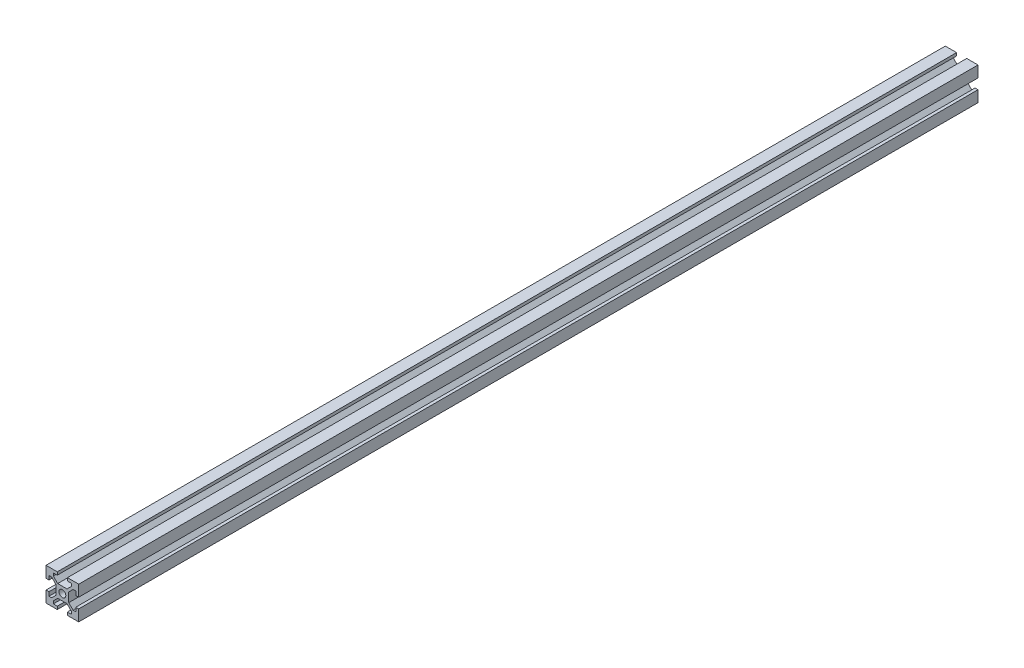
SolidWorks part; units mm, degrees
ref_plane "Front Plane" through (0, 0, 0) normal (0, 0, 1) x (1, 0, 0)
ref_plane "Top Plane" through (0, 0, 0) normal (0, 1, 0) x (1, 0, 0)
ref_plane "Right Plane" through (0, 0, 0) normal (1, 0, 0) x (0, 0, -1)
sketch "Sketch1" plane through (0, 0, 0) normal (0, 0, 1) x (1, 0, 0)
  line L0 (-3.1, 10) -> (-3.1, 8.2007)
  line L1 (-10, 10) -> (-3.1, 10)
  line L2 (-10, 10) -> (-10, 3.1)
  line L3 (-10, -10) -> (-3.1, -10)
  line L4 (10, 10) -> (10, 3.1)
  line L5 (-10, 10) -> (10, -10) construction
  line L6 (-10, -10) -> (10, 10) construction
  line L7 (-3.1, 8.2007) -> (-5.5, 8.2007)
  line L8 (-5.5, 8.2007) -> (-5.5, 6.5607)
  line L9 (-5.5, 6.5607) -> (-2.84, 3.9007)
  line L10 (-2.84, 3.9007) -> (2.84, 3.9007)
  line L11 (2.84, 3.9007) -> (5.5, 6.5607)
  line L12 (5.5, 6.5607) -> (5.5, 8.2007)
  line L13 (5.5, 8.2007) -> (3.1, 8.2007)
  line L14 (3.1, 8.2007) -> (3.1, 10)
  line L15 (-3.1, 8.2007) -> (3.1, 8.2007) construction
  line L16 (-5.5, 6.5607) -> (5.5, 6.5607) construction
  line L17 (3.1, 10) -> (10, 10)
  line L18 (8.2007, 3.1) -> (8.2007, 5.5)
  line L19 (8.2007, 5.5) -> (6.5607, 5.5)
  line L20 (6.5607, 5.5) -> (3.9007, 2.84)
  line L21 (3.9007, 2.84) -> (3.9007, -2.84)
  line L22 (3.9007, -2.84) -> (6.5607, -5.5)
  line L23 (6.5607, -5.5) -> (8.2007, -5.5)
  line L24 (8.2007, -5.5) -> (8.2007, -3.1)
  line L25 (8.2007, 3.1) -> (8.2007, -3.1) construction
  line L26 (6.5607, 5.5) -> (6.5607, -5.5) construction
  line L27 (10, 3.1) -> (8.2007, 3.1)
  line L28 (8.2007, -3.1) -> (10, -3.1)
  line L29 (3.1, -8.2007) -> (5.5, -8.2007)
  line L30 (5.5, -8.2007) -> (5.5, -6.5607)
  line L31 (5.5, -6.5607) -> (2.84, -3.9007)
  line L32 (2.84, -3.9007) -> (-2.84, -3.9007)
  line L33 (-2.84, -3.9007) -> (-5.5, -6.5607)
  line L34 (-5.5, -6.5607) -> (-5.5, -8.2007)
  line L35 (-5.5, -8.2007) -> (-3.1, -8.2007)
  line L36 (3.1, -8.2007) -> (-3.1, -8.2007) construction
  line L37 (5.5, -6.5607) -> (-5.5, -6.5607) construction
  line L38 (3.1, -10) -> (3.1, -8.2007)
  line L39 (-3.1, -8.2007) -> (-3.1, -10)
  line L40 (-8.2007, -3.1) -> (-8.2007, -5.5)
  line L41 (-8.2007, -5.5) -> (-6.5607, -5.5)
  line L42 (-6.5607, -5.5) -> (-3.9007, -2.84)
  line L43 (-3.9007, -2.84) -> (-3.9007, 2.84)
  line L44 (-3.9007, 2.84) -> (-6.5607, 5.5)
  line L45 (-6.5607, 5.5) -> (-8.2007, 5.5)
  line L46 (-8.2007, 5.5) -> (-8.2007, 3.1)
  line L47 (-8.2007, -3.1) -> (-8.2007, 3.1) construction
  line L48 (-6.5607, -5.5) -> (-6.5607, 5.5) construction
  line L49 (-10, -3.1) -> (-8.2007, -3.1)
  line L50 (-8.2007, 3.1) -> (-10, 3.1)
  line L51 (10, -3.1) -> (10, -10)
  line L52 (3.1, -10) -> (10, -10)
  line L53 (-10, -3.1) -> (-10, -10)
  point P0 (0, 0)
  point P8 (0, 8.2007)
  point P18 (0, 3.9007)
  dimension "D1" = 20
  dimension "D2" = 20
  dimension "D3" = 5.68
  dimension "D4" = 6.2
  dimension "D5" = 4.3
  dimension "D6" = 11
  dimension "D7" = 0.75
  dimension "D8" = 4
extrude "Boss-Extrude1" add sketch "Sketch1" along normal blind 550
sketch "Sketch2" plane through (0, 0, 550) normal (0, 0, 1) x (1, 0, 0)
  circle A0 centre (0, 0) radius 2.1
  dimension "D1" = 4.2
extrude "Cut-Extrude1" cut sketch "Sketch2" against normal through all
sketch "Sketch3" plane through (0, 3.9007, 0) normal (0, 1, 0) x (1, 0, 0)
  line L0 (0, 0) -> (0, -550) construction
  line L1 (2.84, -550) -> (-2.84, -550) construction
  circle A0 centre (0, -275) radius 2.1
  dimension "D1" = 4.2
extrude "Cut-Extrude2" cut sketch "Sketch3" against normal through all
